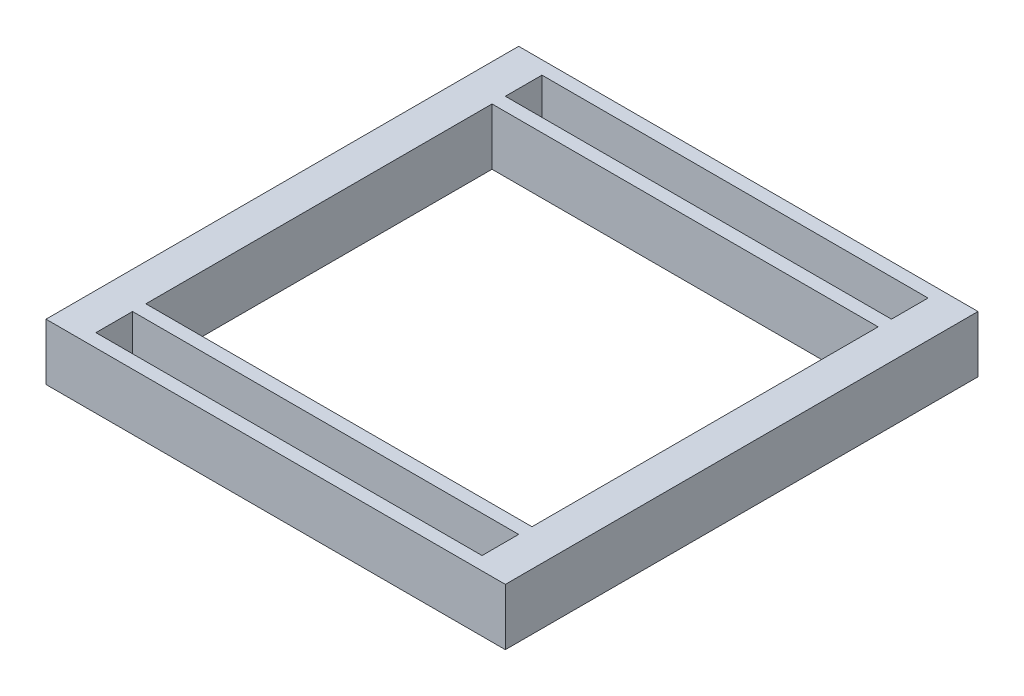
SolidWorks part; units mm, degrees
ref_plane "Front Plane" through (0, 0, 0) normal (0, 0, 1) x (1, 0, 0)
ref_plane "Top Plane" through (0, 0, 0) normal (0, 1, 0) x (1, 0, 0)
ref_plane "Right Plane" through (0, 0, 0) normal (1, 0, 0) x (0, 0, -1)
sketch "Sketch1" plane through (0, 0, 0) normal (0, 1, 0) x (1, 0, 0)
  line L1 (-350.52, -360.68) -> (350.52, -360.68)
  line L2 (-350.52, -360.68) -> (-350.52, 360.68)
  line L3 (-350.52, 360.68) -> (350.52, 360.68)
  line L4 (350.52, -360.68) -> (350.52, 360.68)
  line L5 (-350.52, -360.68) -> (350.52, 360.68) construction
  line L6 (-350.52, 360.68) -> (350.52, -360.68) construction
  line L11 (-294.64, 340.36) -> (294.64, 340.36)
  line L12 (-294.64, 340.36) -> (-294.64, 284.48)
  line L13 (-294.64, 284.48) -> (294.64, 284.48)
  line L14 (294.64, 340.36) -> (294.64, 284.48)
  line L15 (-294.64, 264.16) -> (294.64, 264.16)
  line L16 (-294.64, 264.16) -> (-294.64, -264.16)
  line L17 (-294.64, -264.16) -> (294.64, -264.16)
  line L18 (294.64, 264.16) -> (294.64, -264.16)
  line L23 (-294.64, -284.48) -> (294.64, -284.48)
  line L24 (-294.64, -284.48) -> (-294.64, -340.36)
  line L25 (-294.64, -340.36) -> (294.64, -340.36)
  line L26 (294.64, -284.48) -> (294.64, -340.36)
  point P0 (0, 0)
  dimension "D1" = 701.04
  dimension "D2" = 721.36
  dimension "D3" = 20.32
  dimension "D4" = 55.88
  dimension "D5" = 55.88
  dimension "D6" = 20.32
  dimension "D7" = 20.32
  dimension "D8" = 20.32
  dimension "D9" = 55.88
  dimension "D10" = 55.88
extrude "Boss-Extrude1" add sketch "Sketch1" along normal blind 86.36
